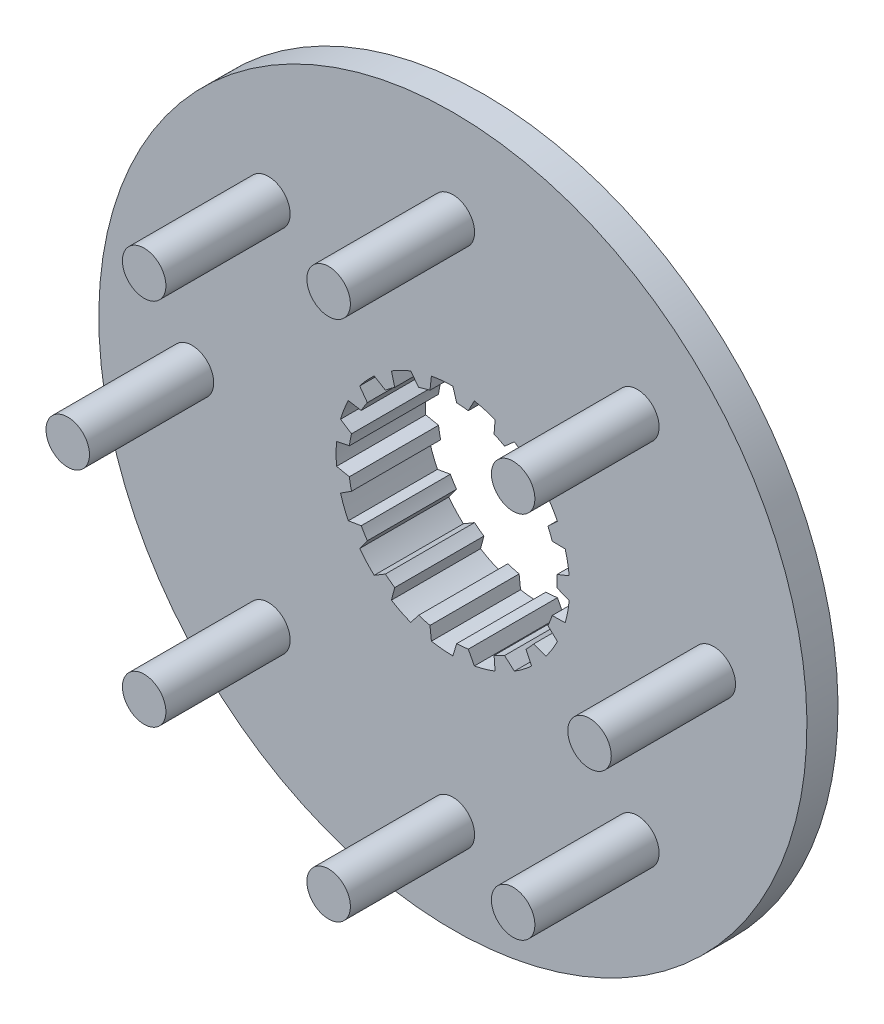
SolidWorks part; units mm, degrees
material "AISI 1045 Steel, cold drawn"
ref_plane "Front Plane" through (0, 0, 0) normal (0, 0, 1) x (1, 0, 0)
ref_plane "Top Plane" through (0, 0, 0) normal (0, 1, 0) x (1, 0, 0)
ref_plane "Right Plane" through (0, 0, 0) normal (1, 0, 0) x (0, 0, -1)
sketch "Sketch1" plane through (0, 0, 0) normal (1, 0, 0) x (0, 0, -1)
  line L0 (0, 0) -> (0, 57)
  line L1 (0, 57) -> (5, 57)
  line L2 (5, 57) -> (5, 25)
  line L3 (5, 25) -> (14.35, 25)
  line L4 (14.35, 25) -> (14.35, 0)
  line L5 (14.35, 0) -> (0, 0)
  dimension "D1" = 57
  dimension "D2" = 14.35
  dimension "D3" = 5
  dimension "D4" = 25
revolve "Revolve1" add sketch "Sketch1" angle 360 about L5
sketch "Sketch2" plane through (0, 0, -14.35) normal (0, 0, -1) x (-1, 0, 0)
  line L0 (0, 0) -> (0, 18.8)
  line L1 (0, 0) -> (3.4545, 18.4799) construction
  line L2 (0, 0) -> (6.7913, 17.5305)
  line L3 (3.4545, 18.4799) -> (3.6857, 16.3907)
  line L4 (5.495, 15.8759) -> (6.7913, 17.5305)
  circle A0 centre (0, 0) radius 18.8 construction
  circle A1 centre (0, 0) radius 16.8 construction
  arc A2 (0, 18.8) -> (3.4545, 18.4799) centre (0, 0) cw
  arc A3 (3.4545, 18.4799) -> (6.7913, 17.5305) centre (0, 0) cw construction
  arc A4 (3.6857, 16.3907) -> (5.495, 15.8759) centre (0, 0) cw
  dimension "D1" = 37.6
  dimension "D3" = 10.588
  dimension "D4" = 10.588
  dimension "D2" = 2
extrude "Cut-Extrude1" cut sketch "Sketch2" against normal through all
pattern_circular "CirPattern1" count 17 over 360 about axis through (0, 0, 0) along (0, 0, 1) of "Cut-Extrude1"
sketch "Sketch3" plane through (0, 0, 0) normal (0, 0, 1) x (1, 0, 0)
  circle A0 centre (0, 0) radius 42 construction
  circle A1 centre (0, 42) radius 3.5
  circle A2 centre (29.6985, 29.6985) radius 3.5
  circle A3 centre (42, 0) radius 3.5
  circle A4 centre (29.6985, -29.6985) radius 3.5
  circle A5 centre (0, -42) radius 3.5
  circle A6 centre (-29.6985, -29.6985) radius 3.5
  circle A7 centre (-42, 0) radius 3.5
  circle A8 centre (-29.6985, 29.6985) radius 3.5
  point P22 (0, 0)
  dimension "D1" = 84
  dimension "D2" = 7
  dimension "D3" = 8
extrude "Boss-Extrude1" add sketch "Sketch3" along normal blind 20
